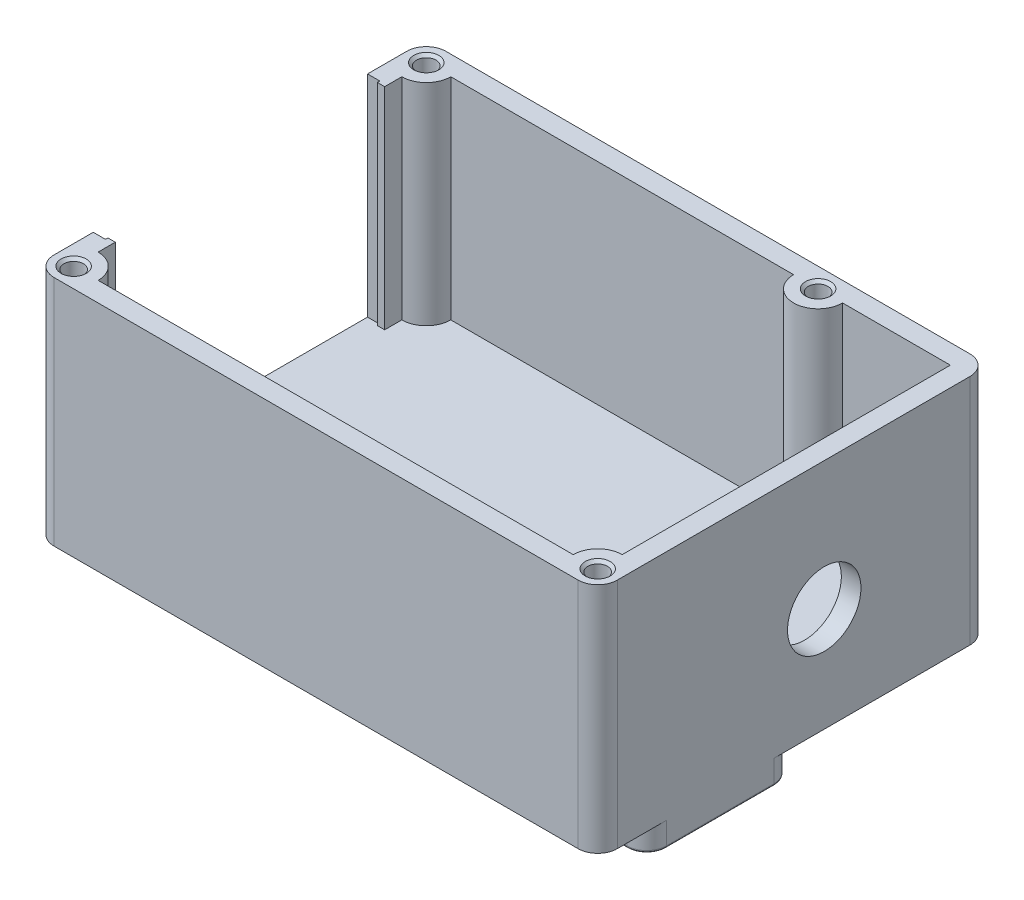
SolidWorks part; units mm, degrees
material "201.0-T7 Insulated Mold Casting (SS)"
ref_plane "Front Plane" through (0, 0, 0) normal (0, 0, 1) x (1, 0, 0)
ref_plane "Top Plane" through (0, 0, 0) normal (0, 1, 0) x (1, 0, 0)
ref_plane "Right Plane" through (0, 0, 0) normal (1, 0, 0) x (0, 0, -1)
sketch "Sketch1" plane through (0, 0, 0) normal (0, 1, 0) x (1, 0, 0)
  line L0 (0, 0) -> (-14, 0) construction
  line L1 (-14, 16) -> (32, 16)
  line L2 (-14, 16) -> (-14, -16)
  line L3 (-14, -16) -> (32, -16)
  line L4 (32, 16) -> (32, -16)
  dimension "D1" = 32
  dimension "D2" = 46
  dimension "D3" = 14
extrude "Boss-Extrude1" add sketch "Sketch1" against normal blind 19
hole_wizard "M2x0.4 Tapped Hole1" positions "Sketch3" profile "Sketch2" tap size "M2x0.4" standard "ANSI Metric"
sketch "Sketch3" plane through (0, 0, 0) normal (0, 1, 0) x (1, 0, 0)
  line L0 (-12.4, 14.4) -> (19.6, 14.4) construction
  line L2 (30.4, -14.4) -> (-12.4, -14.4) construction
  line L4 (-14, 16) -> (-14, -16) construction
  line L5 (32, 16) -> (-14, 16) construction
  line L8 (-14, -16) -> (32, -16) construction
  line L9 (32, -16) -> (32, 16) construction
  line L10 (-12.4, 14.4) -> (-12.4, -14.4) construction
  point P0 (-12.4, 14.4)
  point P2 (19.6, 14.4)
  point P4 (30.4, -14.4)
  point P6 (-12.4, -14.4)
  dimension "D1" = 1.6
  dimension "D2" = 1.6
  dimension "D3" = 1.6
  dimension "D4" = 1.6
  dimension "D5" = 32
sketch "Sketch2" plane through (-12.4, 0, -14.4) normal (1, 0, 0) x (0, 0, 1)
  line L0 (0, 0) -> (0, 6.4807)
  line L1 (0, 6.4807) -> (0.8, 6)
  line L2 (0.8, 6) -> (0.8, 0.225)
  line L3 (0.8, 0.225) -> (1.025, 0)
  line L5 (1.025, 0) -> (0, 0)
  line L6 (-0.8, 0.225) -> (-1.025, 0) construction
  line L10 (0, 6.4807) -> (-0.8, 6) construction
  line L11 (0, -6.35) -> (0, 107.95) construction
  dimension "Tap Drill Dia." = 1.6
  dimension "Tap Drill Depth" = 6
  dimension "Near C'Sink Dia." = 2.05
  dimension "Near C'Sink Angle" = 90
  dimension "Drill Angle" = 118
sketch "Sketch4" plane through (0, -19, 0) normal (0, -1, 0) x (-1, 0, 0)
  line L0 (-12, -5.5) -> (-12, 5.5) construction
  line L1 (0, 0) -> (-12, 0) construction
  circle A0 centre (0, 0) radius 4
  circle A1 centre (-12, -5.5) radius 3.5
  circle A2 centre (-12, 5.5) radius 3.5
  dimension "D1" = 8
  dimension "D4" = 7
  dimension "D2" = 11
  dimension "D3" = 12
extrude "Boss-Extrude2" add sketch "Sketch4" along normal blind 2
sketch "Sketch5" plane through (0, -19, 0) normal (0, 1, 0) x (1, 0, 0)
  line L0 (32, -16) -> (32, 16) construction
  line L1 (19, 0) -> (32, 0)
  line L2 (19, 0) -> (19, -12)
  line L3 (19, -12) -> (32, -12)
  line L4 (32, 0) -> (32, -12)
  line L6 (-14, -16) -> (32, -16) construction
  dimension "D1" = 13
  dimension "D2" = 12
  dimension "D3" = 4
extrude "Boss-Extrude4" add sketch "Sketch5" against normal blind 2
fillet "Fillet1" radius 1.6 4 edges at (-14, -9.5, -16) (32, -9.5, -16) (32, -9.5, 16) (-14, -9.5, 16)
fillet "Fillet2" radius 1.6 4 edges at (32, -20, 12) (19, -20, 12) (19, -20, 0) (32, -20, 0)
fillet "Fillet3" radius 0.2 11 edges at (31.5314, -21, 0.4686) (25.5, -21, 0) (19.4686, -21, 0.4686) (19, -21, 6) (19.4686, -21, 11.5314) (25.5, -21, 12) (31.5314, -21, 11.5314) (32, -21, 6) (12, -21, -9) (12, -21, 2) (0, -21, -4)
sketch "Sketch8" plane through (0, 0, 0) normal (0, 1, 0) x (1, 0, 0)
  line L0 (30.4, 16) -> (-12.4, 16) construction
  line L1 (-10.4, 14.4) -> (17.6, 14.4)
  line L2 (-12.4, 12.4) -> (-12.4, -12.4)
  line L3 (-10.4, -14.4) -> (28.4, -14.4)
  line L4 (30.4, 14.4) -> (30.4, -12.4)
  line L5 (-12.4, 14.4) -> (30.4, -14.4) construction
  line L6 (-12.4, -14.4) -> (30.4, 14.4) construction
  line L7 (-12.4, -16) -> (30.4, -16) construction
  line L8 (32, -14.4) -> (32, 14.4) construction
  line L9 (-14, 14.4) -> (-14, -14.4) construction
  line L10 (21.6, 14.4) -> (30.4, 14.4)
  arc A0 (-12.4, 12.4) -> (-10.4, 14.4) centre (-12.4, 14.4) ccw
  arc A1 (17.6, 14.4) -> (21.6, 14.4) centre (19.6, 14.4) ccw
  arc A2 (30.4, -12.4) -> (28.4, -14.4) centre (30.4, -14.4) ccw
  arc A3 (-10.4, -14.4) -> (-12.4, -12.4) centre (-12.4, -14.4) ccw
  circle A4 centre (-12.4, 14.4) radius 0.8 construction
  circle A5 centre (30.4, -14.4) radius 0.8 construction
  circle A6 centre (-12.4, -14.4) radius 0.8 construction
  point P0 (9, 0)
  dimension "D5" = 4
  dimension "D1" = 1.6
  dimension "D2" = 1.6
  dimension "D3" = 1.6
  dimension "D4" = 1.6
extrude "Cut-Extrude3" cut sketch "Sketch8" against normal offset from surface (17.2 mm away) 1.8 up to face at (12, -19, -2)
sketch "Sketch6" plane through (0, 0, 0) normal (0, 1, 0) x (1, 0, 0)
  line L0 (-14, 14.4) -> (-14, -14.4) construction
  line L1 (-12, 11) -> (-14, 11)
  line L2 (-12, 11) -> (-12, -11)
  line L3 (-12, -11) -> (-14, -11)
  line L4 (-14, 11) -> (-14, -11)
  line L5 (-12, 11) -> (-14, -11) construction
  line L6 (-12, -11) -> (-14, 11) construction
  line L7 (0, 0) -> (-13, 0) construction
  point P0 (-13, 0)
  dimension "D1" = 2
  dimension "D2" = 22
extrude "Cut-Extrude1" cut sketch "Sketch6" against normal offset from surface (17.2 mm away) 1.8 up to face at (12, -19, -2)
sketch "Sketch7" plane through (0, 0, 0) normal (0, 1, 0) x (1, 0, 0)
  line L0 (-14, -11) -> (-14, -14.4) construction
  line L1 (-13, 11.2) -> (-14, 11.2)
  line L2 (-13, 11.2) -> (-13, -11.2)
  line L3 (-13, -11.2) -> (-14, -11.2)
  line L4 (-14, 11.2) -> (-14, -11.2)
  line L5 (-13, 11.2) -> (-14, -11.2) construction
  line L6 (-13, -11.2) -> (-14, 11.2) construction
  line L7 (0, 0) -> (-13.5, 0) construction
  point P0 (-13.5, 0)
  dimension "D1" = 22.4
  dimension "D2" = 1
extrude "Cut-Extrude2" cut sketch "Sketch7" against normal up to surface (17.2 mm away) up to face at (2.3396, -17.2, -1.1396)
sketch "Sketch9" plane through (32, 0, 0) normal (1, 0, 0) x (0, 0, -1)
  line L0 (-14.4, 0) -> (14.4, 0) construction
  line L1 (16, 0) -> (16, -19) construction
  circle A0 centre (2.5, -10.5) radius 3
  dimension "D2" = 6
  dimension "D3" = 13.5
  dimension "D1" = 10.5
extrude "Cut-Extrude4" cut sketch "Sketch9" against normal through all
